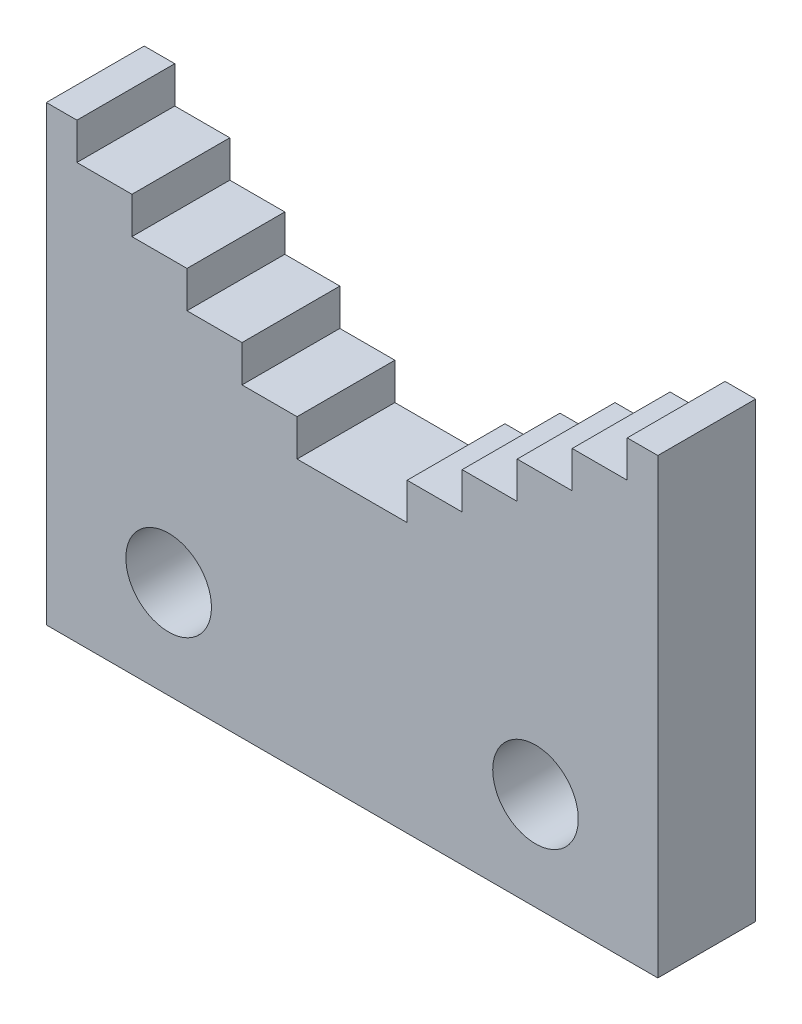
SolidWorks part; units mm, degrees
ref_plane "Front Plane" through (0, 0, 0) normal (0, 0, 1) x (1, 0, 0)
ref_plane "Top Plane" through (0, 0, 0) normal (0, 1, 0) x (1, 0, 0)
ref_plane "Right Plane" through (0, 0, 0) normal (1, 0, 0) x (0, 0, -1)
sketch "Sketch1" plane through (0, 0, 0) normal (0, 0, 1) x (1, 0, 0)
  line L0 (25, 0) -> (-25, 0)
  line L1 (-25, 0) -> (-25, 37)
  line L2 (-25, 37) -> (-22.5, 37)
  line L3 (-22.5, 37) -> (-22.5, 34)
  line L4 (-22.5, 34) -> (-18, 34)
  line L5 (-18, 34) -> (-18, 31)
  line L6 (-18, 31) -> (-13.5, 31)
  line L7 (-13.5, 31) -> (-13.5, 28)
  line L8 (-13.5, 28) -> (-9, 28)
  line L9 (-9, 28) -> (-9, 25)
  line L10 (-9, 25) -> (-4.5, 25)
  line L11 (-4.5, 25) -> (-4.5, 22)
  line L12 (-4.5, 22) -> (4.5, 22)
  line L14 (4.5, 25) -> (4.5, 22)
  line L15 (9, 25) -> (4.5, 25)
  line L16 (9, 28) -> (9, 25)
  line L17 (13.5, 28) -> (9, 28)
  line L18 (13.5, 31) -> (13.5, 28)
  line L19 (18, 31) -> (13.5, 31)
  line L20 (18, 34) -> (18, 31)
  line L21 (22.5, 34) -> (18, 34)
  line L22 (22.5, 37) -> (22.5, 34)
  line L23 (25, 37) -> (22.5, 37)
  line L24 (25, 0) -> (25, 37)
  circle A0 centre (-15, 8) radius 3.5
  circle A1 centre (15, 8) radius 3.5
  dimension "D9" = 7
  dimension "D1" = 4.5
  dimension "D2" = 2.5
  dimension "D3" = 50
  dimension "D4" = 15
  dimension "D5" = 37
  dimension "D6" = 37
  dimension "D7" = 10
  dimension "D8" = 8
extrude "Boss-Extrude1" add sketch "Sketch1" along normal blind 8
